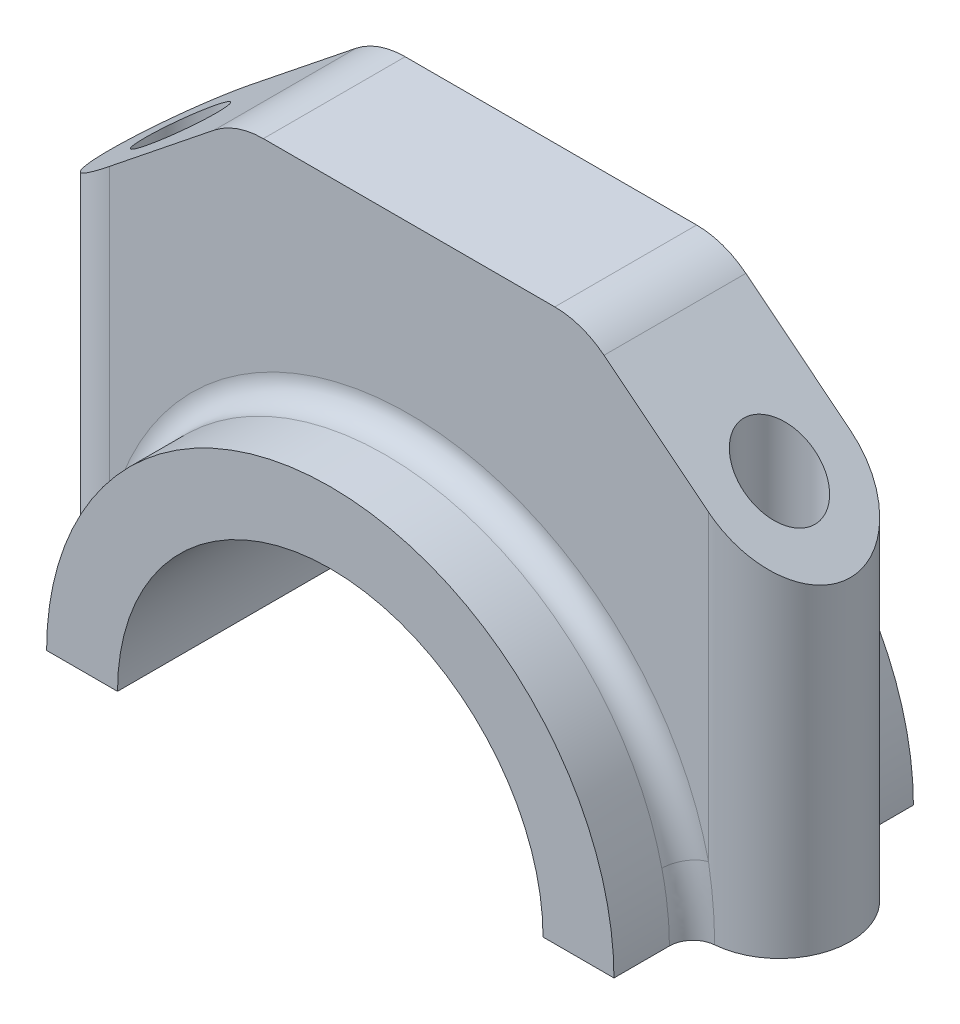
SolidWorks part; units mm, degrees
ref_plane "Front Plane" through (0, 0, 0) normal (0, 0, 1) x (1, 0, 0)
ref_plane "Top Plane" through (0, 0, 0) normal (0, 1, 0) x (1, 0, 0)
ref_plane "Right Plane" through (0, 0, 0) normal (1, 0, 0) x (0, 0, -1)
sketch "Sketch2" plane through (0, 0, 0) normal (0, 0, 1) x (1, 0, 0)
  line L0 (-36, 0) -> (-27, 0)
  line L1 (27, 0) -> (36, 0)
  arc A0 (36, 0) -> (-36, 0) centre (0, 0) ccw
  arc A1 (27, 0) -> (-27, 0) centre (0, 0) ccw
extrude "Boss-Extrude1" add sketch "Sketch2" along normal blind 38
ref_plane "Plane1" through (0, 60, 0) normal (0, -1, 0) x (-1, 0, 0)
sketch "Sketch3" plane through (0, 60, 0) normal (0, -1, 0) x (-1, 0, 0)
  line L0 (36, -19) -> (-36, -19) construction
  line L1 (36, -38) -> (36, 0) construction
  line L2 (-36, -38) -> (-36, 0) construction
  line L3 (0, 0) -> (0, -38) construction
  line L4 (-36, -38) -> (36, -38) construction
  line L5 (38, -19) -> (-38, -19) construction
  line L6 (38, -28) -> (-38, -28)
  line L7 (38, -10) -> (-38, -10)
  arc A0 (38, -28) -> (38, -10) centre (38, -19) ccw
  arc A1 (-38, -10) -> (-38, -28) centre (-38, -19) ccw
  circle A2 centre (38, -19) radius 4.5
  circle A3 centre (-38, -19) radius 4.5
  point P13 (0, -19)
  point P22 (47, -19)
  dimension "D2" = 9
  dimension "D4" = 9
  dimension "D1" = 76
  dimension "D3" = 47
extrude "Boss-Extrude2" add sketch "Sketch3" along normal blind 60
sketch "Sketch4" plane through (0, 0, 28) normal (0, 0, 1) x (1, 0, 0)
  line L1 (-27, 0) -> (27, 0)
  line L2 (-27, 0) -> (27, 0)
  arc A1 (27, 0) -> (-27, 0) centre (0, 0) ccw
  arc A2 (27, 0) -> (-27, 0) centre (0, 0) ccw
  dimension "D1" = 0
extrude "Cut-Extrude1" cut sketch "Sketch4" against normal blind 60
sketch "Sketch5" plane through (0, 0, 28) normal (0, 0, 1) x (1, 0, 0)
  line L0 (-47, 40) -> (-22, 60)
  line L1 (-47, 60) -> (-47, 0) construction
  line L2 (38, 60) -> (-38, 60) construction
  line L3 (0, 70.9765) -> (0, -4.566) construction
  line L4 (47, 40) -> (22, 60)
  line L5 (-47, 40) -> (-47, 60)
  line L6 (-47, 60) -> (-22, 60)
  line L7 (22, 60) -> (47, 60)
  line L8 (-11, 60) -> (11, 60) construction
  line L9 (47, 0) -> (47, 60) construction
  line L10 (47, 60) -> (47, 40)
  dimension "D1" = 25
  dimension "D2" = 20
extrude "Cut-Extrude2" cut sketch "Sketch5" against normal blind 60
fillet "Fillet1" radius 10 2 edges at (-22, 60, 19) (22, 60, 19)
fillet "Fillet2" radius 3 2 edges at (0, 36, 10) (0, 36, 28)
